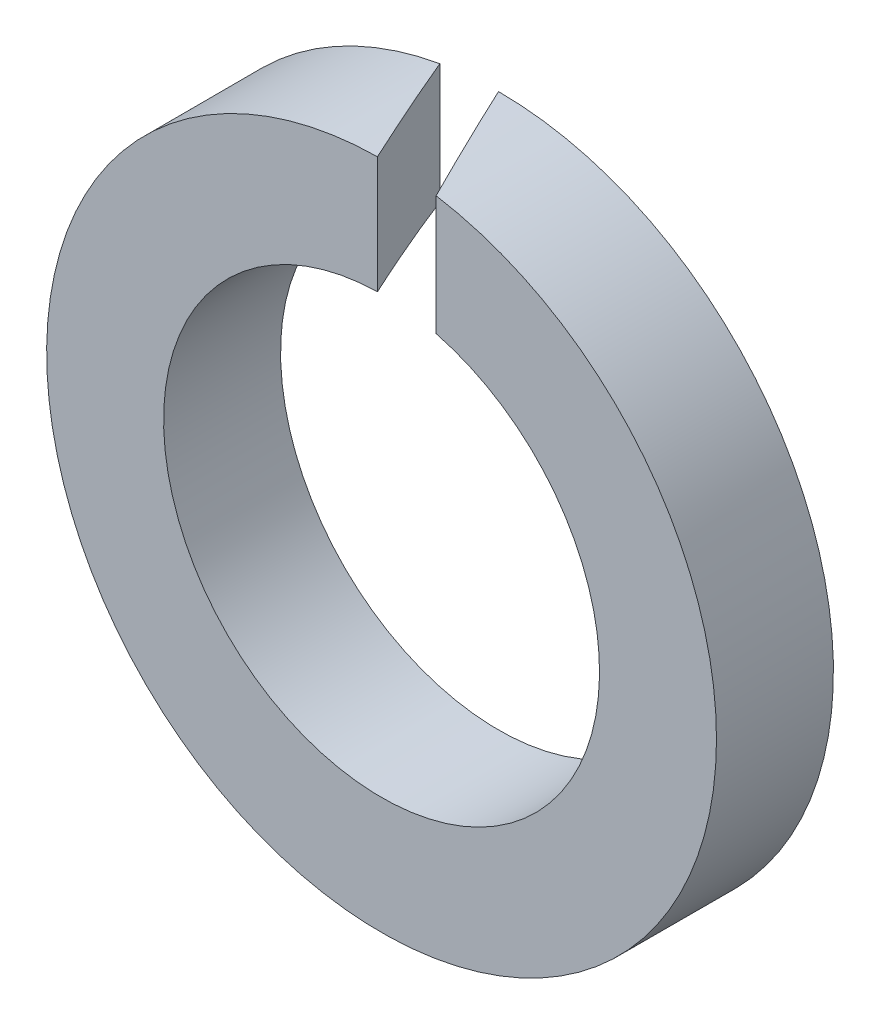
SolidWorks part; units mm, degrees
material "Q235-A"
ref_plane "Front Plane" through (0, 0, 0) normal (0, 0, 1) x (1, 0, 0)
ref_plane "Top Plane" through (0, 0, 0) normal (0, 1, 0) x (1, 0, 0)
ref_plane "Right Plane" through (0, 0, 0) normal (1, 0, 0) x (0, 0, -1)
sketch "草图1" plane through (0, 0, 0) normal (0, 0, 1) x (1, 0, 0)
  circle A0 centre (0, 0) radius 3.15
  circle A1 centre (0, 0) radius 2.05
  dimension "D1" = 4.1
  dimension "D2" = 1.1
extrude "凸台-拉伸1" add sketch "草图1" along normal blind 1.1
sketch "草图2" plane through (0, 0, 0) normal (0, 1, 0) x (1, 0, 0)
  line L0 (0, 0) -> (0.5129, -1.1)
  line L1 (-3.15, -1.1) -> (3.15, -1.1) construction
  line L2 (-0.5517, 0) -> (-0.0388, -1.1)
  line L3 (2.05, 0) -> (-2.05, 0) construction
  line L4 (-0.0388, -1.1) -> (0.5129, -1.1)
  line L5 (-0.5517, 0) -> (0, 0)
  dimension "D1" = 0.5
  dimension "D2" = 65
extrude "切除-拉伸1" cut sketch "草图2" along normal through all
